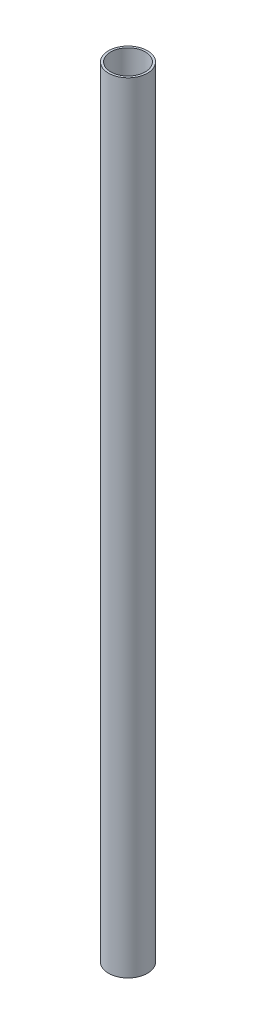
SolidWorks part; units mm, degrees
ref_plane "Front Plane" through (0, 0, 0) normal (0, 0, 1) x (1, 0, 0)
ref_plane "Top Plane" through (0, 0, 0) normal (0, 1, 0) x (1, 0, 0)
ref_plane "Right Plane" through (0, 0, 0) normal (1, 0, 0) x (0, 0, -1)
sketch "Sketch1" plane through (0, 0, 0) normal (0, 1, 0) x (1, 0, 0)
  circle A0 centre (0, 0) radius 6.35
  circle A1 centre (0, 0) radius 5.6388
  dimension "D1" = 12.7
  dimension "D2" = 11.2776
extrude "Boss-Extrude1" add sketch "Sketch1" along normal blind 254
